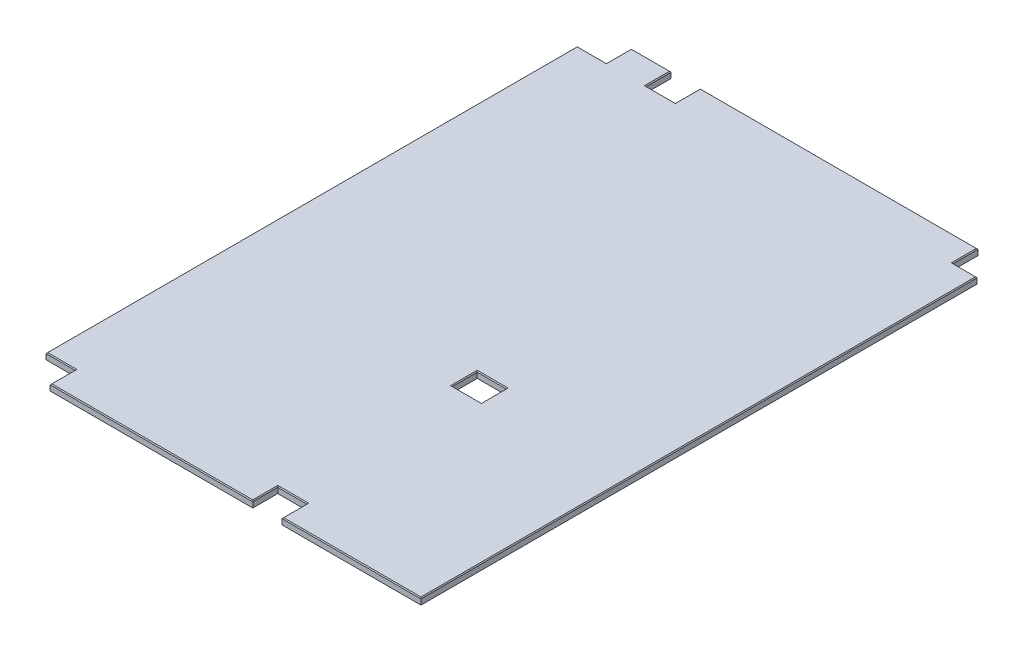
SolidWorks part; units mm, degrees
material "Oak"
ref_plane "Front Plane" through (0, 0, 0) normal (0, 0, 1) x (1, 0, 0)
ref_plane "Top Plane" through (0, 0, 0) normal (0, 1, 0) x (1, 0, 0)
ref_plane "Right Plane" through (0, 0, 0) normal (1, 0, 0) x (0, 0, -1)
sketch "Sketch1" plane through (0, 0, 0) normal (0, 1, 0) x (1, 0, 0)
  line L1 (0, 1771.65) -> (1219.2, 1771.65)
  line L2 (0, 1771.65) -> (0, 0)
  line L3 (0, 0) -> (1219.2, 0)
  line L4 (1219.2, 1771.65) -> (1219.2, 0)
  dimension "D1" = 1771.65
  dimension "D2" = 1219.2
extrude "Boss-Extrude1" add sketch "Sketch1" along normal mid plane 19.05
sketch "Sketch3" plane through (0, 9.525, 0) normal (0, 1, 0) x (1, 0, 0)
  line L0 (0, 1771.65) -> (88.9, 1771.65)
  line L1 (0, 1771.65) -> (0, 1695.45)
  line L2 (0, 1695.45) -> (88.9, 1695.45)
  line L3 (88.9, 1771.65) -> (88.9, 1695.45)
  line L4 (210.1977, 1771.65) -> (299.0977, 1771.65)
  line L5 (210.1977, 1771.65) -> (210.1977, 1695.45)
  line L6 (210.1977, 1695.45) -> (299.0977, 1695.45)
  line L7 (299.0977, 1771.65) -> (299.0977, 1695.45)
  line L20 (706.4756, 684.2125) -> (795.3756, 684.2125)
  line L21 (706.4756, 684.2125) -> (706.4756, 608.0125)
  line L22 (706.4756, 608.0125) -> (795.3756, 608.0125)
  line L23 (795.3756, 684.2125) -> (795.3756, 608.0125)
  line L30 (0, 76.2) -> (88.9, 76.2)
  line L31 (0, 76.2) -> (0, 0)
  line L32 (0, 0) -> (88.9, 0)
  line L33 (88.9, 76.2) -> (88.9, 0)
  line L34 (795.3756, 0) -> (706.4756, 0)
  line L35 (795.3756, 0) -> (795.3756, 76.2)
  line L36 (795.3756, 76.2) -> (706.4756, 76.2)
  line L37 (706.4756, 0) -> (706.4756, 76.2)
  line L46 (0, 1771.65) -> (0, 0) construction
  line L52 (1219.2, 1771.65) -> (0, 1771.65) construction
  line L53 (1219.2, 0) -> (1219.2, 1771.65) construction
  line L55 (1145.5273, 1771.65) -> (1219.2, 1771.65)
  line L56 (1145.5273, 1771.65) -> (1145.5273, 1695.45)
  line L57 (1145.5273, 1695.45) -> (1219.2, 1695.45)
  line L58 (1219.2, 1771.65) -> (1219.2, 1695.45)
  dimension "D1" = 706.4756
  dimension "D2" = 88.9
  dimension "D3" = 88.9
  dimension "D4" = 76.2
  dimension "D5" = 706.4756
  dimension "D6" = 88.9
  dimension "D7" = 608.0125
  dimension "D8" = 76.2
  dimension "D9" = 1695.45
  dimension "D10" = 1145.5273
  dimension "D11" = 210.1977
  dimension "D12" = 88.9
  dimension "D13" = 88.9
other "AlignGroup3"
other "AlignGroup4"
extrude "Cut-Extrude2" cut sketch "Sketch3" against normal through all
chamfer "Chamfer1" distance 2.54 angle 45 22 edges at (750.9256, 9.525, -608.0125) (795.3756, 9.525, -646.1125) (750.9256, 9.525, -684.2125) (706.4756, 9.525, -646.1125) (254.6477, 9.525, -1695.45) (299.0977, 9.525, -1733.55) (722.3125, 9.525, -1771.65) (1219.2, 9.525, -847.725) (1007.2878, 9.525, 0) (795.3756, 9.525, -38.1) (750.9256, 9.525, -76.2) (706.4756, 9.525, -38.1) (397.6878, 9.525, 0) (88.9, 9.525, -38.1) (44.45, 9.525, -76.2) (0, 9.525, -885.825) (44.45, 9.525, -1695.45) (88.9, 9.525, -1733.55) (149.5488, 9.525, -1771.65) (210.1977, 9.525, -1733.55) (1145.5273, 9.525, -1733.55) (1182.3637, 9.525, -1695.45)
